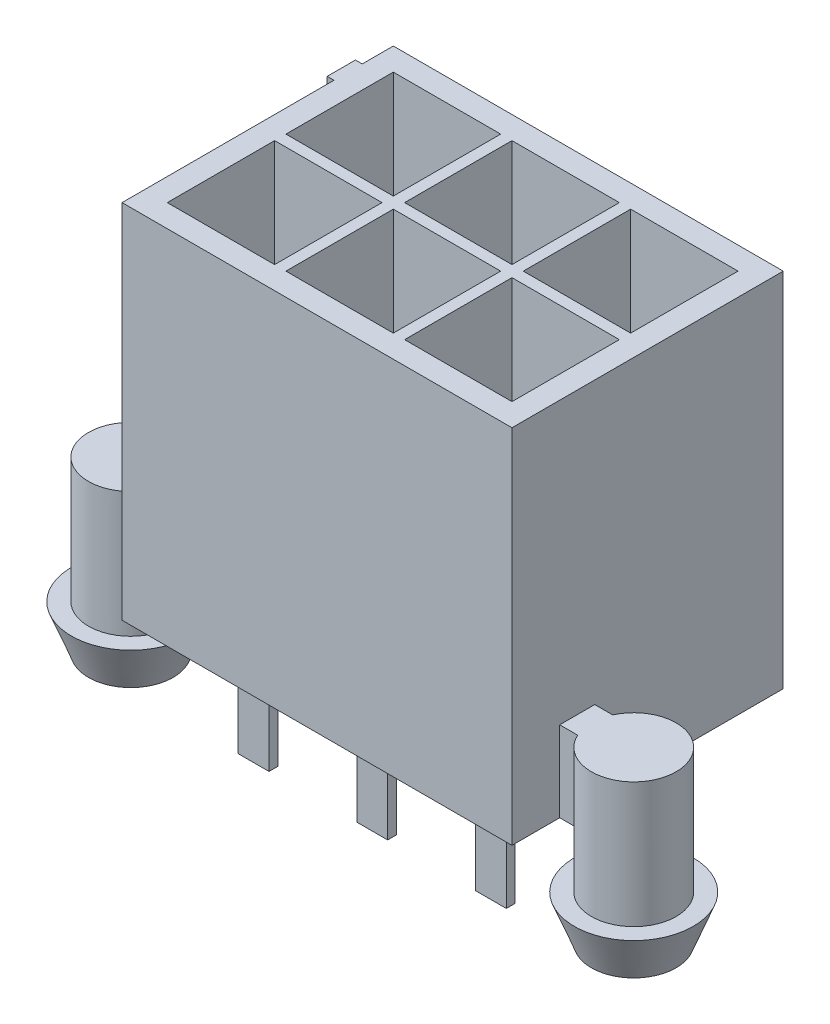
SolidWorks part; units mm, degrees
ref_plane "Front Plane" through (0, 0, 0) normal (0, 0, 1) x (1, 0, 0)
ref_plane "Top Plane" through (0, 0, 0) normal (0, 1, 0) x (1, 0, 0)
ref_plane "Right Plane" through (0, 0, 0) normal (1, 0, 0) x (0, 0, -1)
sketch "Sketch1" plane through (0, 0, 0) normal (0, 1, 0) x (1, 0, 0)
  line L0 (0, 1.85) -> (13.8, 1.85) construction
  line L1 (0, 0) -> (13.8, 0) construction
  line L2 (0, 0) -> (0, 9.6) construction
  line L3 (0, 9.6) -> (13.8, 9.6) construction
  line L4 (13.8, 0) -> (13.8, 9.6) construction
  line L5 (0, 7.35) -> (13.8, 7.35) construction
  line L6 (2.7, 9.6) -> (2.7, 0) construction
  line L7 (6.9, 9.6) -> (6.9, 0) construction
  line L8 (-2, 2.31) -> (15.8, 2.31) construction
  line L9 (11.1, 9.6) -> (11.1, 0) construction
  line L10 (0, 8.5) -> (-0.24, 8.5) construction
  line L11 (-0.24, 8.5) -> (-0.24, 7.5) construction
  line L12 (-0.24, 7.5) -> (0, 7.5) construction
  line L13 (0, 6.7) -> (13.8, 6.7) construction
  line L15 (5.4, 9.6) -> (5.4, 11.01) construction
  line L16 (5.4, 11.01) -> (8.4, 11.01) construction
  line L17 (8.4, 9.6) -> (8.4, 11.01) construction
  line L18 (0, 2.5) -> (13.8, 2.5) construction
  circle A0 centre (-2, 2.31) radius 1.5 construction
  circle A1 centre (15.8, 2.31) radius 1.5 construction
  circle A2 centre (2.7, 7.35) radius 0.7 construction
  circle A3 centre (6.9, 7.35) radius 0.7 construction
  circle A4 centre (11.1, 7.35) radius 0.7 construction
  circle A5 centre (11.1, 1.85) radius 0.7 construction
  circle A6 centre (6.9, 1.85) radius 0.7 construction
  circle A7 centre (2.7, 1.85) radius 0.7 construction
sketch "Sketch3" plane through (0, 0, 0) normal (0, 1, 0) x (1, 0, 0)
  line L0 (13.8, 9.6) -> (0, 9.6)
  line L1 (0, 9.6) -> (0, 8.5)
  line L2 (0, 8.5) -> (-0.24, 8.5)
  line L3 (-0.24, 8.5) -> (-0.24, 7.5)
  line L4 (-0.24, 7.5) -> (0, 7.5)
  line L5 (0, 7.5) -> (0, 0)
  line L6 (0, 0) -> (0, 9.6) construction
  line L10 (0, 0) -> (13.8, 0)
  line L12 (13.8, 0) -> (13.8, 9.6) construction
  line L15 (13.8, 0) -> (13.8, 9.6)
extrude "Boss-Extrude1" add sketch "Sketch3" along normal blind 12.8
ref_plane "Plane1" through (0, 2.85, 0) normal (0, -1, 0) x (-1, 0, 0)
sketch "Sketch4" plane through (0, 2.85, 0) normal (0, 1, 0) x (1, 0, 0)
  line L0 (0, 2.9301) -> (0, 1.6899)
  line L1 (13.8, 2.9301) -> (13.8, 1.6899)
  line L7 (0, 2.9301) -> (-0.6342, 2.9301)
  line L8 (-0.6342, 1.6899) -> (0, 1.6899)
  line L13 (13.8, 1.6899) -> (14.4342, 1.6899)
  line L14 (14.4342, 2.9301) -> (13.8, 2.9301)
  arc A2 (-0.6342, 2.9301) -> (-0.6342, 1.6899) centre (-2, 2.31) ccw
  arc A3 (14.4342, 1.6899) -> (14.4342, 2.9301) centre (15.8, 2.31) ccw
extrude "Boss-Extrude2" add sketch "Sketch4" against normal blind 2.85
sketch "Sketch5" plane through (0, 0, 0) normal (0, -1, 0) x (1, 0, 0)
  circle A0 centre (-2, -2.31) radius 1.5
  circle A1 centre (15.8, -2.31) radius 1.5
extrude "Boss-Extrude3" add sketch "Sketch5" along normal blind 3.16
sketch "Sketch6" plane through (0, -3.16, 0) normal (0, -1, 0) x (1, 0, 0)
  circle A0 centre (-2, -2.31) radius 1.5
  circle A1 centre (15.8, -2.31) radius 1.5
extrude "Boss-Extrude4" add sketch "Sketch6" against normal blind 1.5725 draft 21 draft outward yes
sketch "Sketch9" plane through (0, 12.8, 0) normal (0, 1, 0) x (1, 0, 0)
  line L0 (5, 0.8) -> (8.8, 0.8)
  line L1 (0.8, 0.8) -> (4.6, 0.8)
  line L2 (0.8, 0.8) -> (0.8, 4.6)
  line L3 (0.8, 4.6) -> (4.6, 4.6)
  line L4 (4.6, 0.8) -> (4.6, 4.6)
  line L5 (5, 0.8) -> (5, 4.6)
  line L6 (5, 4.6) -> (8.8, 4.6)
  line L7 (8.8, 0.8) -> (8.8, 4.6)
  line L8 (9.2, 0.8) -> (13, 0.8)
  line L9 (9.2, 0.8) -> (9.2, 4.6)
  line L10 (9.2, 4.6) -> (13, 4.6)
  line L11 (13, 0.8) -> (13, 4.6)
  line L12 (5, 5) -> (8.8, 5)
  line L13 (5, 5) -> (5, 8.8)
  line L14 (5, 8.8) -> (8.8, 8.8)
  line L15 (8.8, 5) -> (8.8, 8.8)
  line L16 (9.2, 5) -> (13, 5)
  line L17 (9.2, 5) -> (9.2, 8.8)
  line L18 (9.2, 8.8) -> (13, 8.8)
  line L19 (13, 5) -> (13, 8.8)
  line L20 (0.8, 5) -> (4.6, 5)
  line L21 (0.8, 5) -> (0.8, 8.8)
  line L22 (0.8, 8.8) -> (4.6, 8.8)
  line L23 (4.6, 5) -> (4.6, 8.8)
  dimension "D1" = 3
  dimension "D2" = 2
ref_plane "Plane2" through (0, 9.11, 0) normal (0, -1, 0) x (-1, 0, 0)
extrude "Cut-Extrude3" cut sketch "Sketch9" against normal blind 9.2
sketch "Sketch10" plane through (0, 9.11, 0) normal (0, -1, 0) x (-1, 0, 0)
  line L0 (-2.7, 9.6) -> (-2.7, 0) construction
  line L7 (-2.155, 1.955) -> (-3.245, 1.955)
  line L8 (-2.155, 1.955) -> (-2.155, 3.045)
  line L9 (-2.155, 3.045) -> (-3.245, 3.045)
  line L10 (-3.245, 1.955) -> (-3.245, 3.045)
  line L11 (-2.155, 1.955) -> (-3.245, 3.045) construction
  line L12 (-2.155, 3.045) -> (-3.245, 1.955) construction
  line L13 (0, 2.5) -> (-13.8, 2.5) construction
  point P5 (-2.7, 2.5)
extrude "Boss-Extrude6" add sketch "Sketch10" along normal blind 13.1 separate body
sketch "Sketch11" plane through (0, 0, -9.6) normal (0, 0, -1) x (-1, 0, 0)
  line L0 (-13.8, 12.8) -> (0, 12.8) construction
  line L1 (-5.4, 12.8) -> (-8.4, 12.8)
  line L2 (-5.4, 12.8) -> (-5.4, 9.8)
  line L3 (-5.4, 9.8) -> (-8.4, 9.8)
  line L4 (-8.4, 12.8) -> (-8.4, 9.8)
extrude "Boss-Extrude7" add sketch "Sketch11" along normal blind 1.4
sketch "Sketch12" plane through (5.4, 0, 0) normal (-1, 0, 0) x (0, 0, 1)
  line L0 (-11, 10.6) -> (-9.6, 12.8)
  line L1 (-11, 9.8) -> (-11, 12.8) construction
  line L2 (-11, 12.8) -> (-9.6, 12.8) construction
  line L3 (-9.6, 12.8) -> (-11, 12.8)
  line L4 (-11, 12.8) -> (-11, 10.6)
extrude "Cut-Extrude4" cut sketch "Sketch12" against normal blind 3
sketch "Sketch13" plane through (2.155, 0, 0) normal (-1, 0, 0) x (0, 0, 1)
  line L0 (-2.2662, -3.99) -> (-2.2662, -0.3271)
  line L1 (-1.955, -3.99) -> (-3.045, -3.99) construction
  line L2 (-3.045, 1.769) -> (-3.045, -3.99)
  line L3 (-3.045, -3.99) -> (-2.2662, -3.99)
  line L4 (-3.045, -3.99) -> (-3.045, 9.11) construction
  line L5 (-2.2662, -0.3271) -> (-3.045, 1.769)
extrude "Cut-Extrude5" cut sketch "Sketch13" against normal blind 1.1
ref_plane "Plane3" through (0, 0, -4.6) normal (0, 0, 1) x (1, 0, 0)
mirror "Mirror2" about plane through (0, 0, -4.6) normal (0, 0, 1) of bodies 144
pattern_linear "LPattern1" count 3 spacing 4.2 along (1, 0, 0) of bodies 146 144
